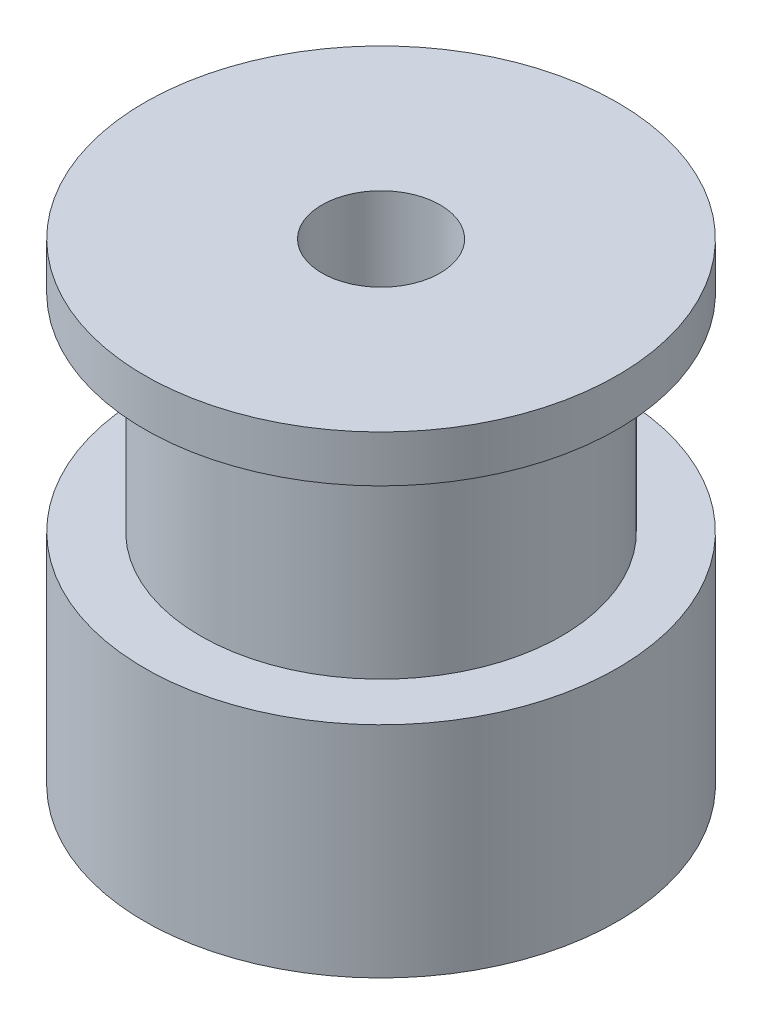
SolidWorks part; units mm, degrees
ref_plane "Front Plane" through (0, 0, 0) normal (0, 0, 1) x (1, 0, 0)
ref_plane "Top Plane" through (0, 0, 0) normal (0, 1, 0) x (1, 0, 0)
ref_plane "Right Plane" through (0, 0, 0) normal (1, 0, 0) x (0, 0, -1)
sketch "Sketch1" plane through (0, 0, 0) normal (0, 0, 1) x (1, 0, 0)
  line L0 (-2, 0) -> (-8, 0)
  line L1 (-8, 0) -> (-8, 7.42)
  line L2 (-8, 7.42) -> (-6.11, 7.42)
  line L3 (-6.11, 7.42) -> (-6.11, 14.42)
  line L4 (-6.11, 14.42) -> (-8, 14.42)
  line L5 (-8, 14.42) -> (-8, 16)
  line L6 (-8, 16) -> (-2, 16)
  line L7 (-2, 16) -> (-2, 0)
  line L8 (0, 0) -> (0, 6.9089) construction
  point P9 (-2, 1.0307)
  dimension "D1" = 2
  dimension "D2" = 8
  dimension "D3" = 16
  dimension "D4" = 7.42
  dimension "D5" = 7
  dimension "D6" = 6.11
  dimension "D7" = 8
revolve "Revolve1" add sketch "Sketch1" angle 360 about L8
